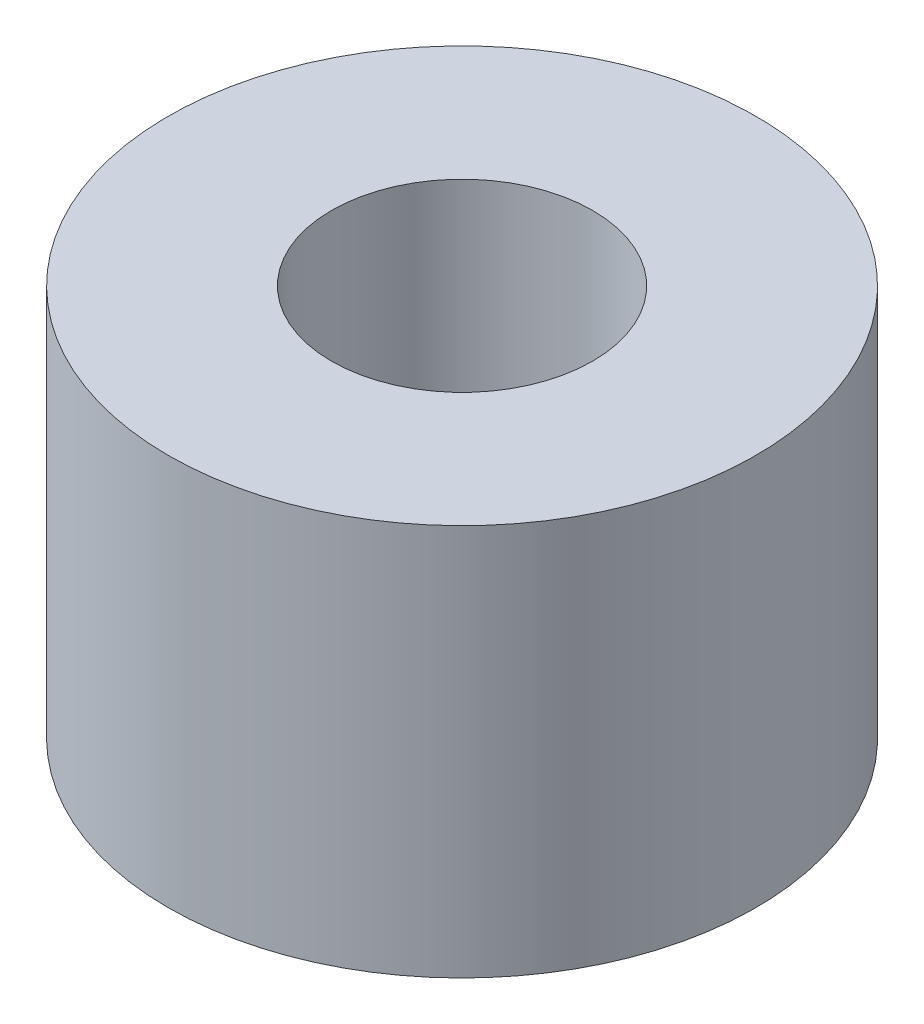
SolidWorks part; units mm, degrees
ref_plane "Front Plane" through (0, 0, 0) normal (0, 0, 1) x (1, 0, 0)
ref_plane "Top Plane" through (0, 0, 0) normal (0, 1, 0) x (1, 0, 0)
ref_plane "Right Plane" through (0, 0, 0) normal (1, 0, 0) x (0, 0, -1)
sketch "Sketch1" plane through (0, 0, 0) normal (0, 1, 0) x (1, 0, 0)
  circle A0 centre (0, 0) radius 2.54
  circle A1 centre (0, 0) radius 5.715
  dimension "D1" = 5.08
  dimension "D2" = 11.43
extrude "Boss-Extrude1" add sketch "Sketch1" along normal blind 7.62
